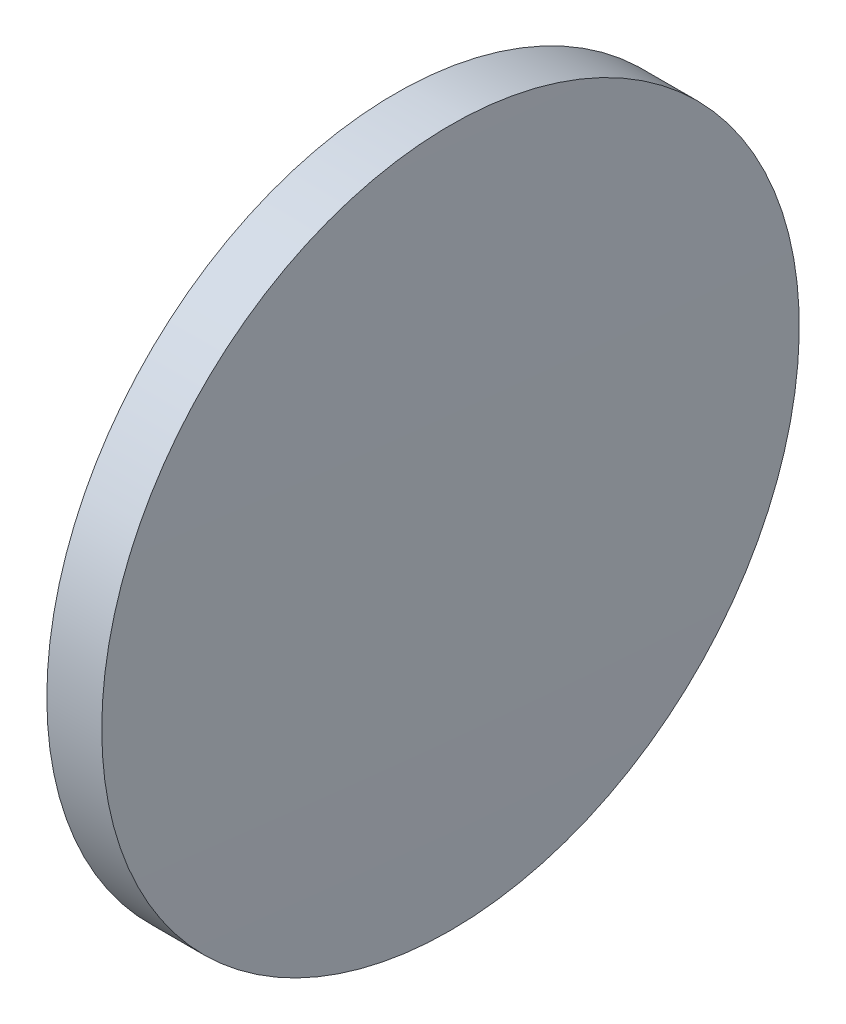
SolidWorks part; units mm, degrees
ref_plane "前视基准面" through (0, 0, 0) normal (0, 0, 1) x (1, 0, 0)
ref_plane "上视基准面" through (0, 0, 0) normal (0, 1, 0) x (1, 0, 0)
ref_plane "右视基准面" through (0, 0, 0) normal (1, 0, 0) x (0, 0, -1)
sketch "草图1" plane through (0, 0, 0) normal (0, 0, 1) x (1, 0, 0)
  line L0 (497.8102, 171.1403) -> (516.6062, 171.1403) construction
  line L1 (503.5484, 171.1403) -> (503.5484, 183.8403)
  line L2 (505.6484, 171.1403) -> (503.5484, 171.1403)
  line L5 (503.5484, 183.8403) -> (505.5484, 183.8403)
  arc A0 (505.6484, 171.1403) -> (505.5484, 183.8403) centre (-300.8516, 171.1403) ccw
revolve "旋转1" add sketch "草图1" angle 360 about L0
